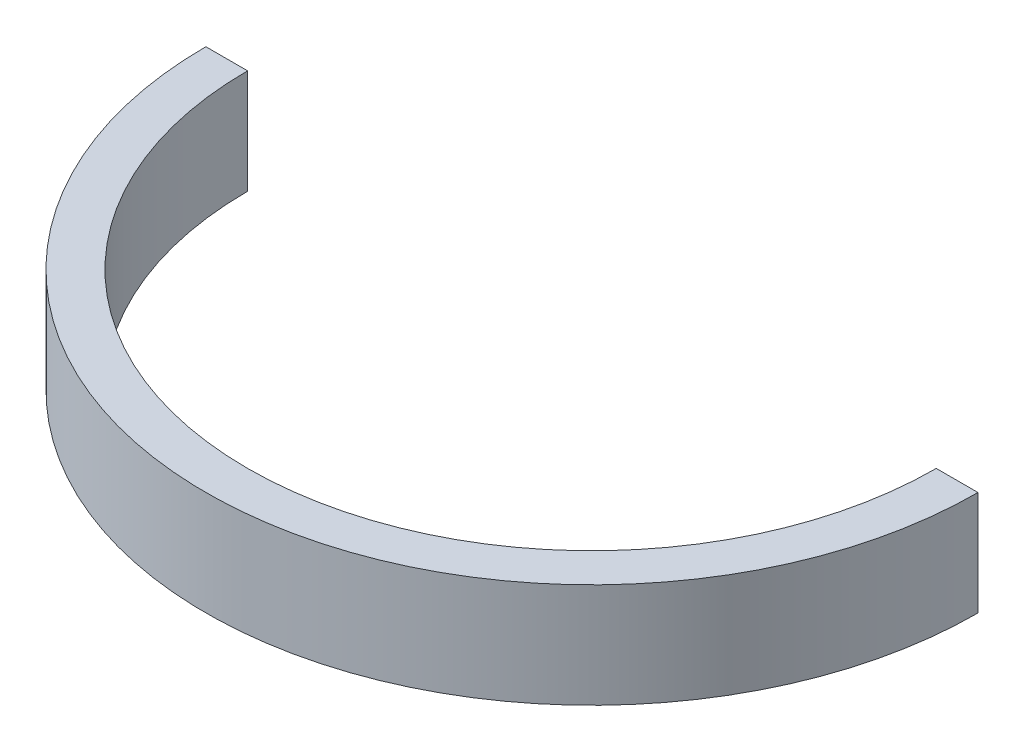
SolidWorks part; units mm, degrees
ref_plane "Front" through (0, 0, 0) normal (0, 0, 1) x (1, 0, 0)
ref_plane "Top" through (0, 0, 0) normal (0, 1, 0) x (1, 0, 0)
ref_plane "Right" through (0, 0, 0) normal (1, 0, 0) x (0, 0, -1)
sketch "草图1" plane through (0, 0, 0) normal (0, 1, 0) x (1, 0, 0)
  line L0 (-74, 0) -> (-66, 0)
  line L1 (66, 0) -> (74, 0)
  arc A0 (-74, 0) -> (74, 0) centre (0, 0) ccw
  arc A1 (-66, 0) -> (66, 0) centre (0, 0) ccw
extrude "凸台-拉伸1" add sketch "草图1" along normal blind 20
